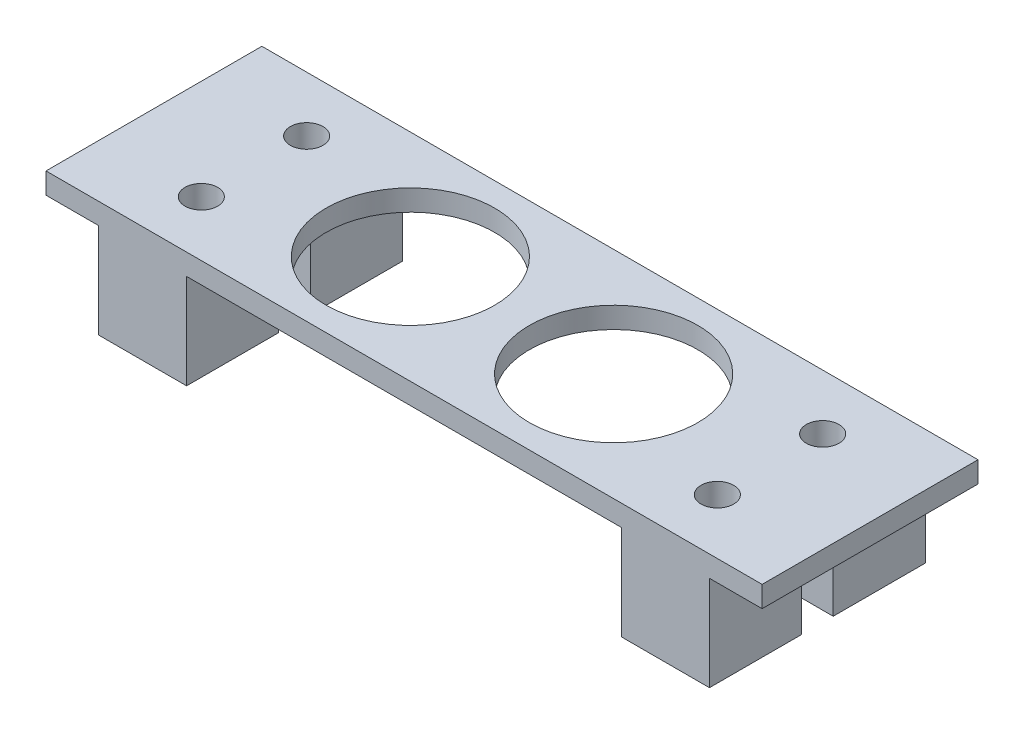
SolidWorks part; units mm, degrees
ref_plane "Front Plane" through (0, 0, 0) normal (0, 0, 1) x (1, 0, 0)
ref_plane "Top Plane" through (0, 0, 0) normal (0, 1, 0) x (1, 0, 0)
ref_plane "Right Plane" through (0, 0, 0) normal (1, 0, 0) x (0, 0, -1)
sketch "Sketch2" plane through (0, 0, 0) normal (0, 1, 0) x (1, 0, 0)
  line L0 (-24.5, 5) -> (-24.5, -5) construction
  line L1 (-29, 10.25) -> (29, 10.25)
  line L2 (-29, 10.25) -> (-29, -10.25)
  line L3 (-29, -10.25) -> (29, -10.25)
  line L4 (29, 10.25) -> (29, -10.25)
  line L5 (-29, 10.25) -> (29, -10.25) construction
  line L6 (-29, -10.25) -> (29, 10.25) construction
  line L7 (-24.5, -5) -> (24.5, -5) construction
  line L8 (24.5, -5) -> (24.5, 5) construction
  line L9 (24.5, 5) -> (-24.5, 5) construction
  line L10 (-20.65, 10.25) -> (-20.65, -10.25) construction
  line L15 (20.65, 10.25) -> (20.65, -10.25) construction
  line L16 (-20.65, 0) -> (20.65, 0) construction
  circle A0 centre (-9.65, 0) radius 8
  circle A1 centre (-24.5, 5) radius 1.55
  circle A2 centre (-24.5, -5) radius 1.55
  circle A3 centre (24.5, 5) radius 1.55
  circle A4 centre (24.5, -5) radius 1.55
  circle A5 centre (9.65, 0) radius 8
  point P0 (0, 0)
  point P16 (-24.5, 0)
  point P17 (0, 5)
  point P27 (0, 0)
  dimension "D1" = 16
  dimension "D2" = 3.1
  dimension "D9" = 41.3
  dimension "D10" = 11
  dimension "D3" = 4.5
  dimension "D4" = 10
  dimension "D5" = 49
  dimension "D6" = 20.5
  dimension "D7" = 11
extrude "Boss-Extrude1" add sketch "Sketch2" along normal blind 2
sketch "Sketch3" plane through (0, 0, 0) normal (0, -1, 0) x (1, 0, 0)
  line L0 (-20.65, 10.25) -> (-20.65, -10.25)
  line L1 (-29, 10.25) -> (29, 10.25) construction
  line L2 (-29, -10.25) -> (29, -10.25) construction
  line L3 (-20.65, -10.25) -> (-29, -10.25)
  line L4 (-29, -10.25) -> (-29, 10.25)
  line L5 (-29, 10.25) -> (-20.65, 10.25)
  line L6 (20.65, 10.25) -> (20.65, -10.25)
  line L7 (20.65, -10.25) -> (29, -10.25)
  line L8 (29, -10.25) -> (29, 10.25)
  line L9 (29, 10.25) -> (20.65, 10.25)
  line L10 (-29, 10.25) -> (29, 10.25) construction
  line L12 (-29, 1.5) -> (-20.65, 1.5)
  line L13 (-29, 1.5) -> (-29, -1.5)
  line L14 (-29, -1.5) -> (-20.65, -1.5)
  line L15 (-20.65, 1.5) -> (-20.65, -1.5)
  line L16 (20.65, 1.5) -> (29, 1.5)
  line L17 (20.65, 1.5) -> (20.65, -1.5)
  line L18 (20.65, -1.5) -> (29, -1.5)
  line L19 (29, 1.5) -> (29, -1.5)
  circle A0 centre (-24.5, -5) radius 1.55
  circle A1 centre (-24.5, 5) radius 1.55
  circle A2 centre (24.5, -5) radius 1.55
  circle A3 centre (24.5, 5) radius 1.55
  point P43 (20.65, 0)
  point P44 (-20.65, 0)
  circle M5 centre (24.5, 5) radius 1.55
  circle M6 centre (24.5, -5) radius 1.55
  circle M7 centre (-24.5, 5) radius 1.55
  circle M8 centre (-24.5, -5) radius 1.55
  line M13 (29, -10.25) -> (29, 10.25)
  line M14 (29, 10.25) -> (-29, 10.25)
  line M15 (-29, 10.25) -> (-29, -10.25)
  line M16 (-29, -10.25) -> (29, -10.25)
  dimension "D1" = 3
extrude "Boss-Extrude2" add sketch "Sketch3" along normal blind 9 contours L12 L0 M15 M14 M7 | L14 L0 M15 M16 M8 | L6 L16 L8 M14 M5 | L18 L6 M16 M13 M6
sketch "Sketch4" plane through (0, 2, 0) normal (0, 1, 0) x (1, 0, 0)
  line L18 (-29, 1.5) -> (-29, 10.25) construction
  line L19 (-29, -10.25) -> (-34, -10.25)
  line L20 (-29, -10.25) -> (-29, 10.25)
  line L21 (-29, 10.25) -> (-34, 10.25)
  line L22 (-34, -10.25) -> (-34, 10.25)
  line L23 (29, 10.25) -> (29, 1.5) construction
  line L24 (29, -10.25) -> (34, -10.25)
  line L25 (29, -10.25) -> (29, 10.25)
  line L26 (29, 10.25) -> (34, 10.25)
  line L27 (34, -10.25) -> (34, 10.25)
  point P5 (29, 10.25)
  point P18 (-29, 10.25)
  point P23 (29, 10.25)
  dimension "D1" = 5
extrude "Boss-Extrude3" add sketch "Sketch4" against normal blind 2
